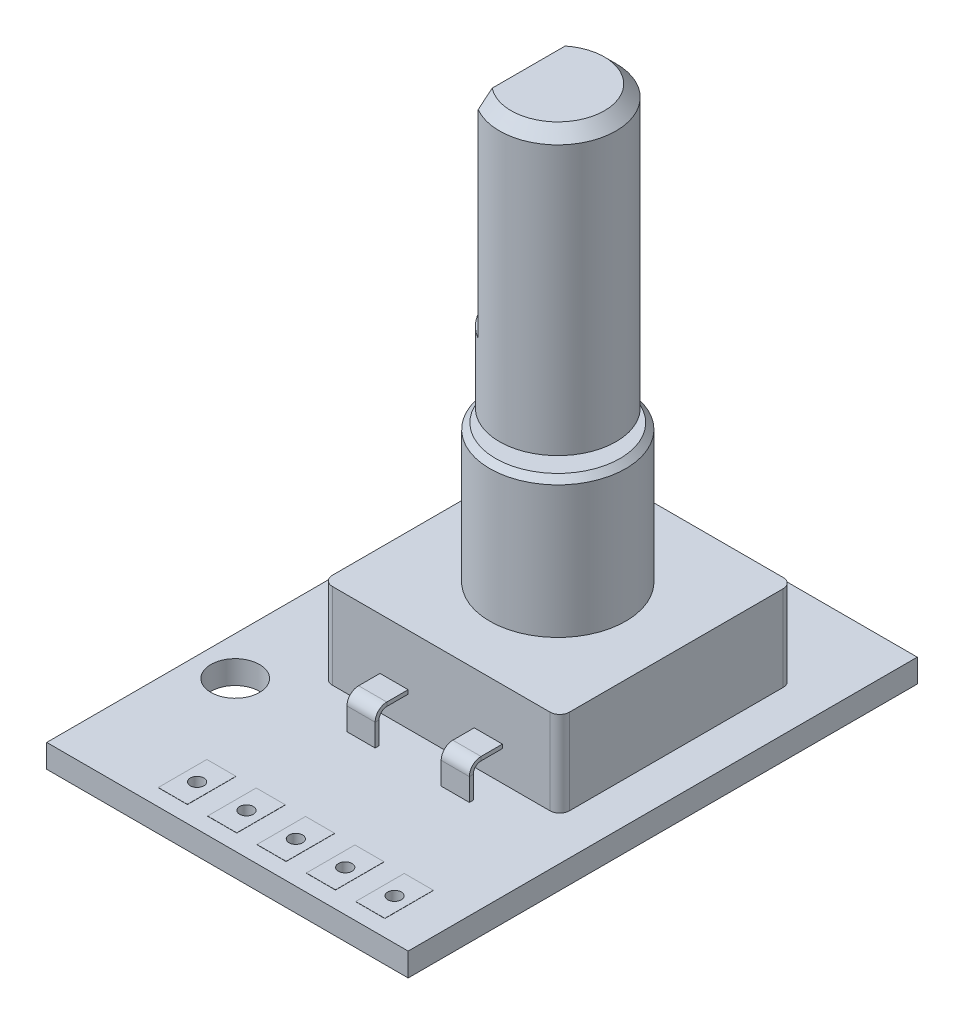
SolidWorks part; units mm, degrees
ref_plane "Front Plane" through (0, 0, 0) normal (0, 0, 1) x (1, 0, 0)
ref_plane "Top Plane" through (0, 0, 0) normal (0, 1, 0) x (1, 0, 0)
ref_plane "Right Plane" through (0, 0, 0) normal (1, 0, 0) x (0, 0, -1)
sketch "Sketch1" plane through (0, 0, 0) normal (0, 1, 0) x (1, 0, 0)
  line L0 (-7.3, 8.3) -> (-7.3, -5.4) construction
  line L1 (-9.3, 13.1) -> (9.3, 13.1)
  line L2 (-9.3, 13.1) -> (-9.3, -13.1)
  line L3 (-9.3, -13.1) -> (9.3, -13.1)
  line L4 (9.3, 13.1) -> (9.3, -13.1)
  line L5 (-9.3, 13.1) -> (9.3, -13.1) construction
  line L6 (-9.3, -13.1) -> (9.3, 13.1) construction
  circle A0 centre (-7.3, 8.3) radius 1.25
  circle A1 centre (-7.3, -5.4) radius 1.25
  point P0 (0, 0)
  dimension "D3" = 2.5
  dimension "D1" = 18.6
  dimension "D2" = 26.2
  dimension "D4" = 13.7
  dimension "D5" = 4.8
  dimension "D6" = 2
extrude "Boss-Extrude1" add sketch "Sketch1" along normal blind 1.2
sketch "Sketch3" plane through (0, 1.2, 0) normal (0, 1, 0) x (1, 0, 0)
  line L0 (9.3, -13.1) -> (9.3, 13.1) construction
  line L1 (-5, -3.2) -> (7.2, -3.2)
  line L2 (-5, -3.2) -> (-5, 8.8)
  line L3 (-5, 8.8) -> (7.2, 8.8)
  line L4 (7.2, -3.2) -> (7.2, 8.8)
  line L5 (-5, -3.2) -> (7.2, 8.8) construction
  line L6 (-5, 8.8) -> (7.2, -3.2) construction
  line L7 (9.3, 13.1) -> (-9.3, 13.1) construction
  point P0 (1.1, 2.8)
  dimension "D1" = 12
  dimension "D2" = 12.2
  dimension "D3" = 2.1
  dimension "D4" = 4.3
extrude "Boss-Extrude2" add sketch "Sketch3" along normal blind 4.4
sketch3d "3DSketch5"
  line L0 (1.1, 5.6, 3.2) -> (1.1, 1.2, 3.2) construction
  line L7 (-5, 5.6, 3.2) -> (7.2, 5.6, 3.2) construction
  line L8 (-5, 1.2, 3.2) -> (7.2, 1.2, 3.2) construction
  line L9 (-1.325, 2.85, 3.2) -> (-1.325, 2.85, 4.3)
  line L10 (-1.325, 2.35, 4.8) -> (-1.325, 1.2, 4.8)
  arc A0 (-1.325, 2.85, 4.3) -> (-1.325, 2.35, 4.8) centre (-1.325, 2.35, 4.3) ccw
  point P0 (-1.325, 2.85, 3.2)
  point P15 (-1.325, 2.85, 4.8)
  point P16 (-0.825, 2.35, 4.3)
  dimension "D3" = 0.5
  dimension "D1" = 2.425
  dimension "D2" = 1.65
  dimension "D5" = 1.6
sketch "Sketch10" plane through (0, 0, 3.2) normal (0, 0, 1) x (1, 0, 0)
  line L1 (-2.05, 2.75) -> (-0.6, 2.75)
  line L2 (-2.05, 2.75) -> (-2.05, 2.95)
  line L3 (-2.05, 2.95) -> (-0.6, 2.95)
  line L4 (-0.6, 2.75) -> (-0.6, 2.95)
  line L5 (-2.05, 2.75) -> (-0.6, 2.95) construction
  line L6 (-2.05, 2.95) -> (-0.6, 2.75) construction
  point P0 (-1.325, 2.85)
  dimension "D1" = 1.45
  dimension "D2" = 0.2
sweep "Sweep3" add profiles "Sketch10" path "3DSketch5"
ref_plane "Plane4" through (1.1, 0, 0) normal (-1, 0, 0) x (0, 0, 1)
mirror "Mirror2" about plane through (1.1, 0, 0) normal (-1, 0, 0) of "Sweep3"
sketch "Sketch13" plane through (0, 0, -8.8) normal (0, 0, -1) x (-1, 0, 0)
  line L0 (-1.1, 5.6) -> (-1.1, 1.2) construction
  line L1 (-1.825, 2.7) -> (-0.375, 2.7)
  line L2 (-1.825, 2.7) -> (-1.825, 2.9)
  line L3 (-1.825, 2.9) -> (-0.375, 2.9)
  line L4 (-0.375, 2.7) -> (-0.375, 2.9)
  line L5 (-1.825, 2.7) -> (-0.375, 2.9) construction
  line L6 (-1.825, 2.9) -> (-0.375, 2.7) construction
  line L7 (-7.2, 5.6) -> (5, 5.6) construction
  line L8 (-7.2, 1.2) -> (5, 1.2) construction
  point P0 (-1.1, 2.8)
  dimension "D1" = 1.45
  dimension "D2" = 0.2
  dimension "D5" = 1.6
sketch3d "3DSketch6"
  line L2 (1.1, 2.8, -8.8) -> (1.1, 2.8, -9.75)
  line L6 (1.1, 2.3, -10.25) -> (1.1, 1.2, -10.25)
  arc A0 (1.1, 2.8, -9.75) -> (1.1, 2.3, -10.25) centre (1.1, 2.3, -9.75) ccw
  point P2 (1.1, 2.8, -10.25)
  point P5 (0.6, 2.3, -9.75)
  dimension "D2" = 0.5
  dimension "D1" = 1.45
sweep "Sweep4" add profiles "Sketch13" path "3DSketch6"
pattern_linear "LPattern1" count 2 spacing 2.85 along (-1, 0, 0) of "Sweep4"
pattern_linear "LPattern2" count 2 spacing 2.85 along (1, 0, 0) of "Sweep4"
sketch "Sketch14" plane through (0, 5.6, 0) normal (0, 1, 0) x (1, 0, 0)
  line L0 (-5, 8.8) -> (7.2, -3.2) construction
  line L1 (-5, -3.2) -> (7.2, 8.8) construction
  circle A0 centre (1.1, 2.8) radius 3.5
  dimension "D1" = 7
extrude "Boss-Extrude4" add sketch "Sketch14" along normal blind 7.1
chamfer "Chamfer1" distance 0.3 angle 45 1 edges at (1.1, 12.7, 0.7)
sketch "Sketch15" plane through (0, 12.7, 0) normal (0, 1, 0) x (1, 0, 0)
  circle A2 centre (1.1, 2.8) radius 1.9
  circle A3 centre (1.1, 2.8) radius 1.9
  dimension "D1" = 1.3
extrude "Boss-Extrude5" add sketch "Sketch15" along normal blind 0.65
sketch "Sketch16" plane through (0, 13.35, 0) normal (0, 1, 0) x (1, 0, 0)
  circle A0 centre (1.1, 2.8) radius 3
  dimension "D1" = 6
extrude "Boss-Extrude6" add sketch "Sketch16" along normal blind 14.45
chamfer "Chamfer2" distance 0.6 angle 45 1 edges at (1.1, 27.8, 0.2)
sketch "Sketch17" plane through (0, 27.8, 0) normal (0, 1, 0) x (1, 0, 0)
  line L0 (-0.3967, 5.4) -> (-0.3967, 0.2)
  circle A1 centre (1.1, 2.8) radius 3
  arc A2 (-0.3967, 5.4) -> (-0.3967, 0.2) centre (1.1, 2.8) ccw
  dimension "D2" = 5.2
  dimension "D1" = 0
extrude "Cut-Extrude1" cut sketch "Sketch17" against normal blind 10.8
sketch "Sketch18" plane through (0, 1.2, 0) normal (0, 1, 0) x (1, 0, 0)
  line L0 (-9.3, -13.1) -> (9.3, -13.1) construction
  line L1 (9.3, -13.1) -> (9.3, 13.1) construction
  circle A0 centre (6.5, -11) radius 0.35
  circle A1 centre (3.96, -11) radius 0.35
  circle A2 centre (1.42, -11) radius 0.35
  circle A3 centre (-1.12, -11) radius 0.35
  circle A4 centre (-3.66, -11) radius 0.35
  dimension "D1" = 0.7
  dimension "D2" = 2.1
  dimension "D3" = 2.8
  dimension "D4" = 5
extrude "Cut-Extrude2" cut sketch "Sketch18" against normal up to surface (1.2 mm away) up to face at (0, 0, 0)
sketch "Sketch19" plane through (0, 1.2, 0) normal (0, 1, 0) x (1, 0, 0)
  line L0 (4.71, -12.25) -> (4.71, -9.75)
  line L1 (5.75, -12.25) -> (7.25, -12.25)
  line L2 (5.75, -12.25) -> (5.75, -9.75)
  line L3 (5.75, -9.75) -> (7.25, -9.75)
  line L4 (7.25, -12.25) -> (7.25, -9.75)
  line L5 (5.75, -12.25) -> (7.25, -9.75) construction
  line L6 (5.75, -9.75) -> (7.25, -12.25) construction
  line L7 (3.21, -9.75) -> (4.71, -9.75)
  line L8 (3.21, -12.25) -> (3.21, -9.75)
  line L9 (3.21, -12.25) -> (4.71, -12.25)
  line L10 (2.17, -12.25) -> (2.17, -9.75)
  line L11 (0.67, -9.75) -> (2.17, -9.75)
  line L12 (0.67, -12.25) -> (0.67, -9.75)
  line L13 (0.67, -12.25) -> (2.17, -12.25)
  line L14 (-0.37, -12.25) -> (-0.37, -9.75)
  line L15 (-1.87, -9.75) -> (-0.37, -9.75)
  line L16 (-1.87, -12.25) -> (-1.87, -9.75)
  line L17 (-1.87, -12.25) -> (-0.37, -12.25)
  line L18 (-2.91, -12.25) -> (-2.91, -9.75)
  line L19 (-4.41, -9.75) -> (-2.91, -9.75)
  line L20 (-4.41, -12.25) -> (-4.41, -9.75)
  line L21 (-4.41, -12.25) -> (-2.91, -12.25)
  circle A0 centre (6.5, -11) radius 0.35
  circle A1 centre (3.96, -11) radius 0.35
  circle A2 centre (1.42, -11) radius 0.35
  circle A3 centre (-1.12, -11) radius 0.35
  circle A4 centre (-3.66, -11) radius 0.35
  point P0 (6.5, -11)
  dimension "D3" = 5
  dimension "D1" = 2.5
  dimension "D2" = 1.5
extrude "Boss-Extrude7" add sketch "Sketch19" along normal blind 0.01
ref_plane "Plane5" through (0, 0.6, 0) normal (0, 1, 0) x (1, 0, 0)
mirror "Mirror3" about plane through (0, 0.6, 0) normal (0, 1, 0) of "Boss-Extrude7"
fillet "Fillet1" radius 0.5 4 edges at (-5, 3.4, -8.8) (-5, 3.4, 3.2) (7.2, 3.4, 3.2) (7.2, 3.4, -8.8)
